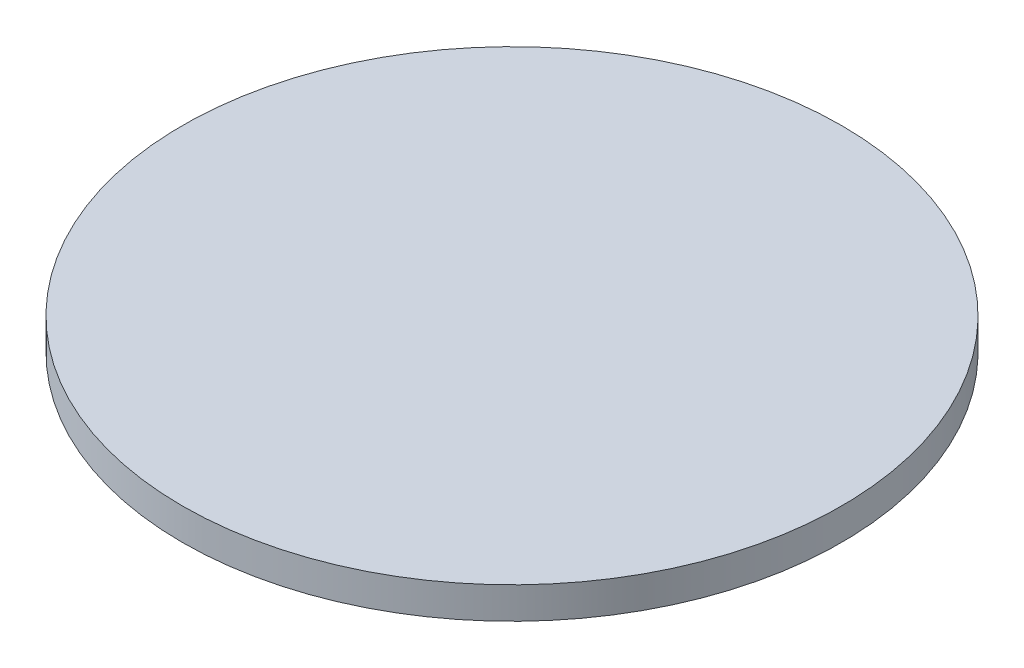
SolidWorks part; units mm, degrees
material "Phenolic-Sheet"
ref_plane "Front Plane" through (0, 0, 0) normal (0, 0, 1) x (1, 0, 0)
ref_plane "Top Plane" through (0, 0, 0) normal (0, 1, 0) x (1, 0, 0)
ref_plane "Right Plane" through (0, 0, 0) normal (1, 0, 0) x (0, 0, -1)
sketch "Sketch1" plane through (0, 0, 0) normal (0, 1, 0) x (1, 0, 0)
  circle A0 centre (0, 0) radius 33.0835
  dimension "D1" = 66.167
extrude "Boss-Extrude1" add sketch "Sketch1" along normal blind 3.175
